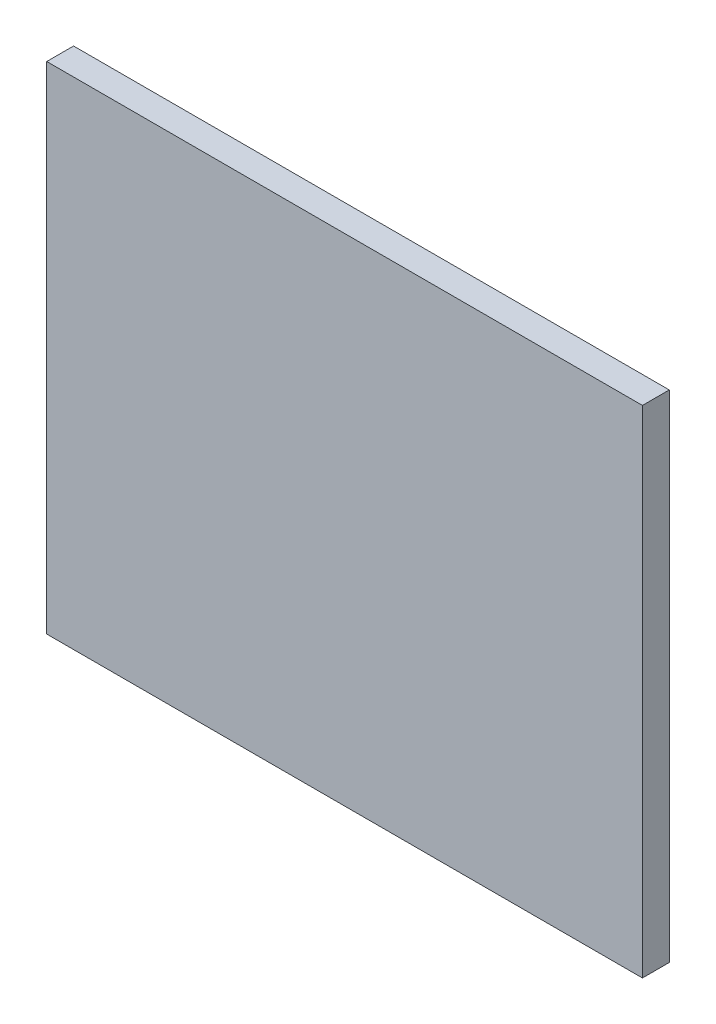
SolidWorks part; units mm, degrees
ref_plane "Alzado" through (0, 0, 0) normal (0, 0, 1) x (1, 0, 0)
ref_plane "Planta" through (0, 0, 0) normal (0, 1, 0) x (1, 0, 0)
ref_plane "Vista lateral" through (0, 0, 0) normal (1, 0, 0) x (0, 0, -1)
sketch "Croquis1" plane through (0, 0, 0) normal (0, 0, 1) x (1, 0, 0)
  line L1 (0, 0) -> (111, 0)
  line L2 (0, 0) -> (0, 92.4)
  line L3 (0, 92.4) -> (111, 92.4)
  line L4 (111, 0) -> (111, 92.4)
  dimension "D1" = 92.4
  dimension "D2" = 111
extrude "Saliente-Extruir1" add sketch "Croquis1" along normal blind 5
